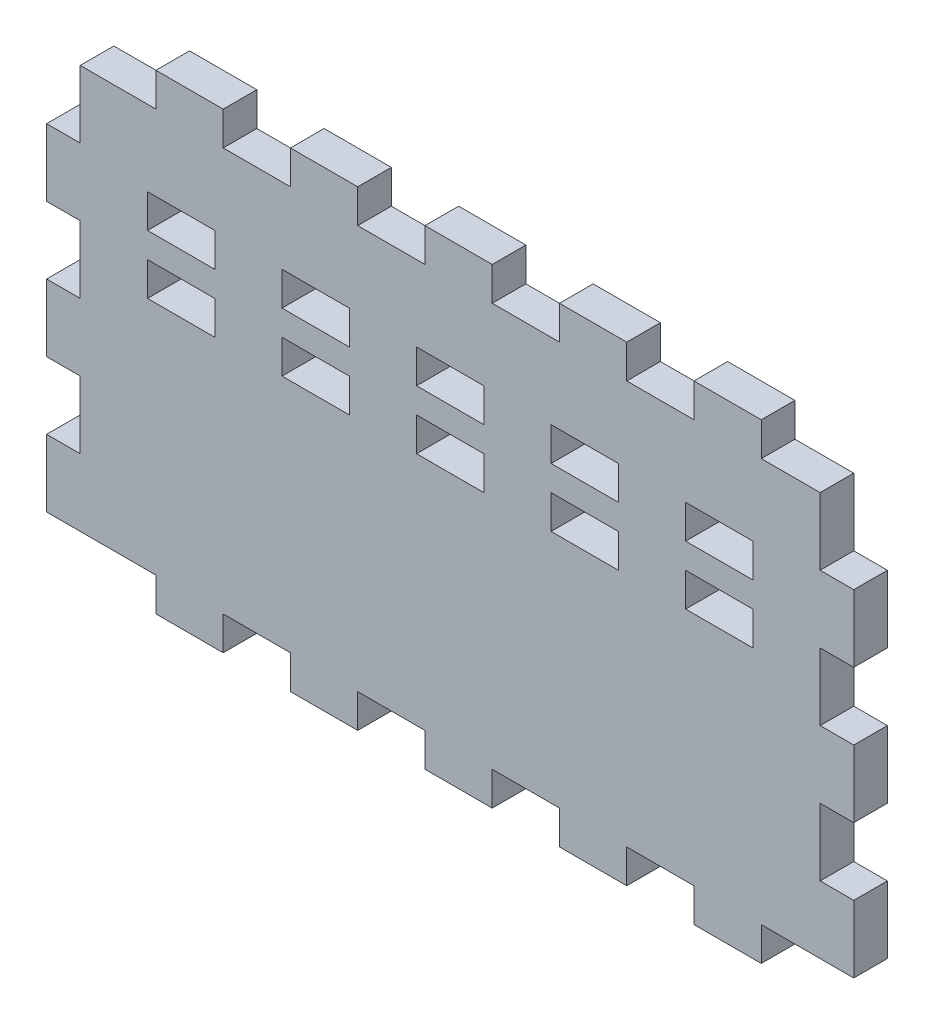
SolidWorks part; units mm, degrees
ref_plane "Front Plane" through (0, 0, 0) normal (0, 0, 1) x (1, 0, 0)
ref_plane "Top Plane" through (0, 0, 0) normal (0, 1, 0) x (1, 0, 0)
ref_plane "Right Plane" through (0, 0, 0) normal (1, 0, 0) x (0, 0, -1)
sketch "Sketch1" plane through (0, 0, 0) normal (0, 0, 1) x (1, 0, 0)
  line L1 (-139.7, -76.2) -> (139.7, -76.2)
  line L2 (-139.7, -76.2) -> (-139.7, 76.2)
  line L3 (-139.7, 76.2) -> (139.7, 76.2)
  line L4 (139.7, -76.2) -> (139.7, 76.2)
  line L5 (-139.7, -76.2) -> (139.7, 76.2) construction
  line L6 (-139.7, 76.2) -> (139.7, -76.2) construction
  point P0 (0, 0)
  dimension "D1" = 279.4
  dimension "D2" = 152.4
extrude "Boss-Extrude1" add sketch "Sketch1" along normal blind 12.7
sketch "Sketch2" plane through (0, -76.2, 0) normal (0, -1, 0) x (1, 0, 0)
  line L0 (-139.7, 0) -> (139.7, 0) construction
  line L1 (-111.125, 0) -> (-85.725, 0)
  line L2 (-111.125, 0) -> (-111.125, 12.7)
  line L3 (-111.125, 12.7) -> (-85.725, 12.7)
  line L4 (-85.725, 0) -> (-85.725, 12.7)
  line L5 (-139.7, 12.7) -> (139.7, 12.7) construction
  line L6 (-139.7, 12.7) -> (-139.7, 0) construction
  dimension "D1" = 28.575
  dimension "D2" = 25.4
extrude "Boss-Extrude2" add sketch "Sketch2" along normal blind 12.7
pattern_linear "LPattern1" count 5 spacing 50.8 along (1, 0, 0) of "Boss-Extrude2"
mirror "Mirror1" about plane through (0, 0, 0) normal (0, 1, 0) of "LPattern1", "Boss-Extrude2"
sketch "Sketch3" plane through (139.7, 0, 0) normal (1, 0, 0) x (0, 0, -1)
  line L0 (0, 83.82) -> (0, -83.82) construction
  line L1 (-12.7, -76.2) -> (0, -76.2)
  line L2 (-12.7, -76.2) -> (-12.7, -50.8)
  line L3 (-12.7, -50.8) -> (0, -50.8)
  line L4 (0, -76.2) -> (0, -50.8)
  dimension "D1" = 25.4
extrude "Boss-Extrude3" add sketch "Sketch3" along normal blind 12.7
pattern_linear "LPattern2" count 3 spacing 50.8 along (0, 1, 0) of "Boss-Extrude3"
mirror "Mirror2" about plane through (0, 0, 0) normal (1, 0, 0) of "LPattern2", "Boss-Extrude3"
sketch "Sketch4" plane through (0, 0, 12.7) normal (0, 0, 1) x (1, 0, 0)
  line L0 (-139.7, 25.4) -> (-139.7, 0) construction
  line L1 (-88.9, 12.7) -> (-114.3, 12.7)
  line L2 (-88.9, 12.7) -> (-88.9, 25.4)
  line L3 (-88.9, 25.4) -> (-114.3, 25.4)
  line L4 (-114.3, 12.7) -> (-114.3, 25.4)
  line L5 (-85.725, -76.2) -> (-60.325, -76.2) construction
  line L6 (-152.4, -76.2) -> (-111.125, -76.2) construction
  line L7 (-114.3, 34.925) -> (-88.9, 34.925)
  line L8 (-114.3, 34.925) -> (-114.3, 47.625)
  line L9 (-114.3, 47.625) -> (-88.9, 47.625)
  line L10 (-88.9, 34.925) -> (-88.9, 47.625)
  point P8 (-73.025, -76.2)
  dimension "D1" = 25.4
  dimension "D2" = 12.7
  dimension "D3" = 25.4
  dimension "D4" = 88.9
  dimension "D5" = 12.7
  dimension "D6" = 25.4
  dimension "D7" = 123.825
extrude "Cut-Extrude1" cut sketch "Sketch4" against normal through all
pattern_linear "LPattern3" count 5 spacing 50.8 along (1, 0, 0) of "Cut-Extrude1"
